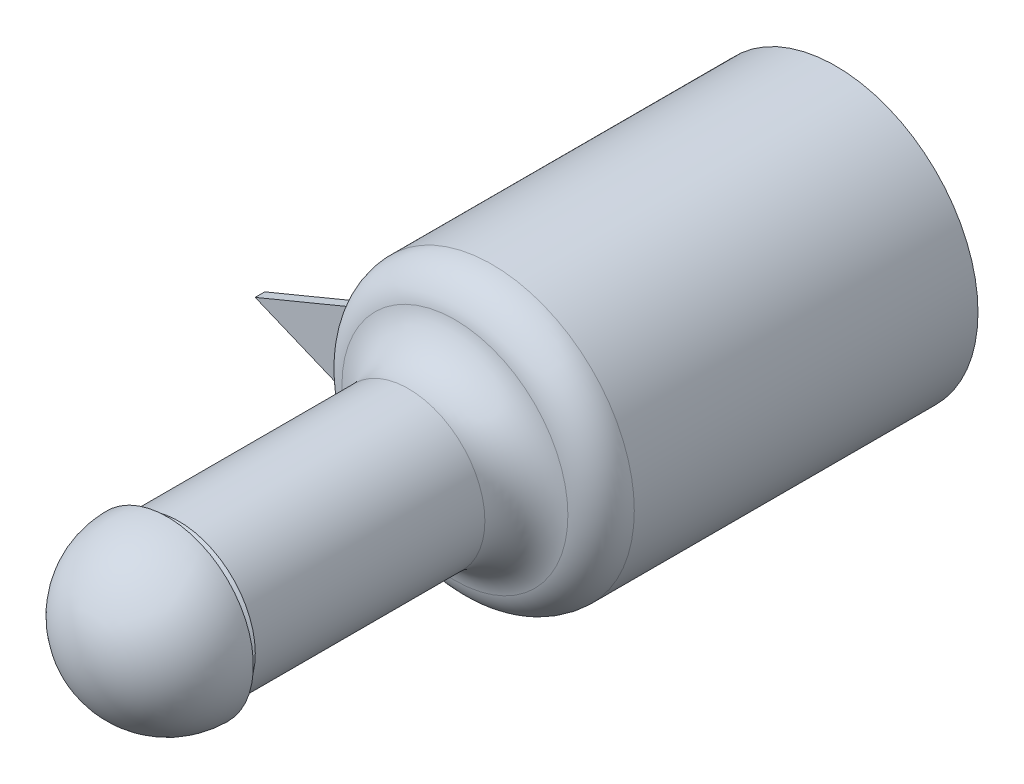
SolidWorks part; units mm, degrees
material "Cast Carbon Steel"
ref_plane "Front Plane" through (0, 0, 0) normal (0, 0, 1) x (1, 0, 0)
ref_plane "Top Plane" through (0, 0, 0) normal (0, 1, 0) x (1, 0, 0)
ref_plane "Right Plane" through (0, 0, 0) normal (1, 0, 0) x (0, 0, -1)
sketch "Sketch2" plane through (0, 0, 0) normal (0, 0, 1) x (1, 0, 0)
  circle A0 centre (0, 0) radius 7.45
  dimension "D1" = 14.9
extrude "Boss-Extrude1" add sketch "Sketch2" along normal mid plane 20
sketch "Sketch3" plane through (0, 0, 10) normal (0, 0, 1) x (1, 0, 0)
  circle A0 centre (0, 0) radius 4
  dimension "D1" = 8
extrude "Boss-Extrude2" add sketch "Sketch3" along normal blind 15
sketch "Sketch4" plane through (0, 0, 25) normal (0, 0, 1) x (1, 0, 0)
  line L0 (0, 4.5) -> (0, -4.5)
  arc A0 (0, 4.5) -> (0, -4.5) centre (0, 0) ccw
  dimension "D1" = 9
fillet "Fillet7" radius 2 1 edges at (7.45, 0, 10)
fillet "Fillet12" radius 2.5 1 edges at (4, 0, 10)
revolve "Revolve1" add sketch "Sketch4" angle 180 about L0
sketch "Sketch17" plane through (0, 0, 0) normal (1, 0, 0) x (0, 0, -1)
  line L0 (-22.4217, 0) -> (7.4619, 0) construction
sketch "Sketch18" plane through (0, 0, 0) normal (0, 1, 0) x (1, 0, 0)
  line L0 (4, -25) -> (4, -12.3758) construction
  line L1 (4, -25) -> (3.2, -25)
  line L2 (4, -25) -> (4, -24.4)
  line L5 (4.5, -25) -> (-4.5, -25) construction
  line L6 (4, -24.4) -> (3.2, -25)
  dimension "D1" = 0.6
  dimension "D2" = 0.8
revolve "Cut-Revolve18" cut sketch "Sketch18" angle 360 about L0
sketch "Sketch19" plane through (0, 0, 0) normal (0, 1, 0) x (1, 0, 0)
  line L2 (-1.5, -24.1) -> (-1.5, -20.4)
  line L3 (-1.5, -20.4) -> (1.5, -20.4)
  line L4 (1.5, -24.1) -> (1.5, -20.4)
  line L5 (-1.1675, -24.7) -> (1.17, -24.7)
  line L7 (0, -22.4217) -> (0, 7.4619) construction
  line L9 (4, -24.4) -> (-4, -24.4) construction
  line L10 (-1.5, -24.1) -> (-1.1675, -24.7)
  line L11 (1.17, -24.7) -> (1.5, -24.1)
  dimension "D1" = 3
  dimension "D2" = 4
  dimension "D3" = 0.3325
  dimension "D4" = 0.33
  dimension "D5" = 1.5
  dimension "D6" = 0.6
  dimension "D7" = 24.7
extrude "Cut-Extrude4" cut sketch "Sketch19" against normal blind 1 from offset 3.5 offset against normal yes
sketch "Sketch20" plane through (0, 0, 0) normal (0, 1, 0) x (1, 0, 0)
  line L0 (0, -22.4217) -> (0, 7.4619) construction
  line L2 (7.45, -8) -> (-7.45, -8) construction
  circle A0 centre (0, -2) radius 1
  dimension "D1" = 2
  dimension "D2" = 6
extrude "Cut-Extrude5" cut sketch "Sketch20" against normal blind 5 from offset 5 offset against normal yes
ref_plane "Plane3" through (0, 0, 8) normal (0, 0, 1) x (1, 0, 0)
sketch "Sketch24" plane through (0, 0, 8) normal (0, 0, 1) x (1, 0, 0)
  line L0 (-7.1563, 2.0711) -> (-12.1563, 0)
  line L1 (-12.1563, 0) -> (-7.1563, -2.0711)
  circle A0 centre (0, 0) radius 7.45 construction
  arc A1 (-7.1563, 2.0711) -> (-7.1563, -2.0711) centre (0, 0) ccw
  point P2 (-12.0182, 2.4995)
  point P5 (-12.1563, 0)
  dimension "D1" = 45
  dimension "D2" = 5
  dimension "D3" = 5
sketch "Sketch26" plane through (0, 0, -10) normal (0, 0, -1) x (-1, 0, 0)
  line L0 (3.2, 2.4) -> (3.2, -2.4)
  arc A0 (3.2, 2.4) -> (3.2, -2.4) centre (0, 0) ccw
  dimension "D1" = 8
  dimension "D2" = 4.8
extrude "Boss-Extrude3" add sketch "Sketch24" along normal mid plane 0.5 separate body
extrude "Cut-Extrude6" cut sketch "Sketch26" against normal blind 15
